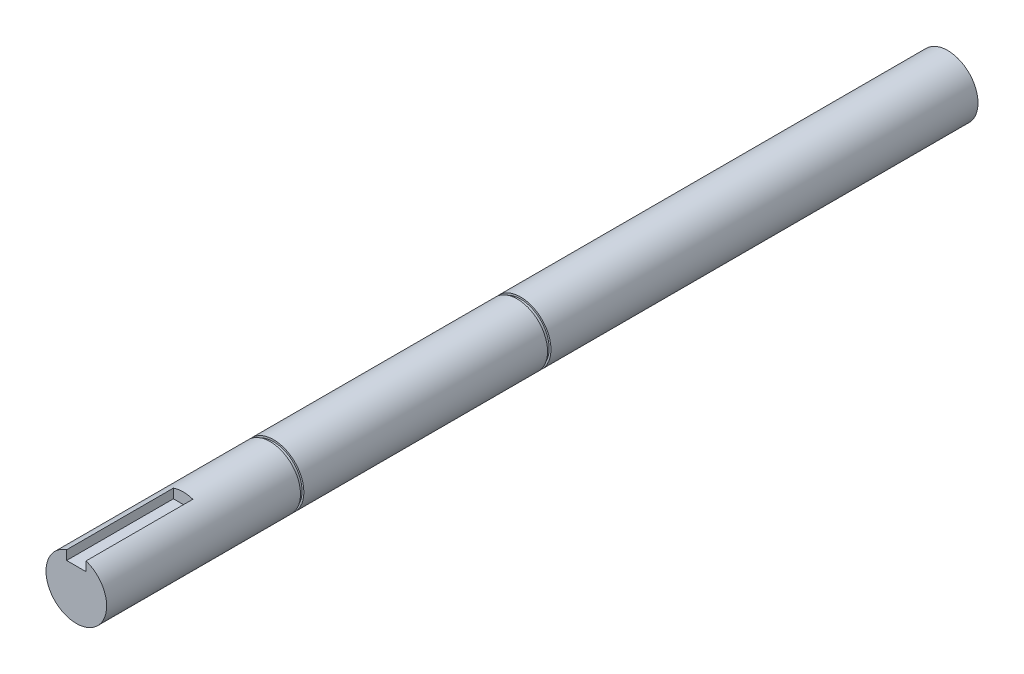
SolidWorks part; units mm, degrees
material "AISI 1020"
ref_plane "Спереди" through (0, 0, 0) normal (0, 0, 1) x (1, 0, 0)
ref_plane "Сверху" through (0, 0, 0) normal (0, 1, 0) x (1, 0, 0)
ref_plane "Справа" through (0, 0, 0) normal (1, 0, 0) x (0, 0, -1)
sketch "Эскиз1" plane through (0, 0, 0) normal (0, 0, 1) x (1, 0, 0)
  circle A0 centre (0, 0) radius 12.5 construction
  circle A1 centre (0, 0) radius 12.5
extrude "Бобышка-Вытянуть1" add sketch "Эскиз1" against normal blind 359 contours A1
sketch "Эскиз2" plane through (0, 0, 0) normal (0, 0, 1) x (1, 0, 0)
  line L0 (-4, 16.5) -> (-4, 8)
  line L1 (-4, 8) -> (4, 8)
  line L2 (4, 8) -> (4, 16.5)
  line L3 (4, 16.5) -> (-4, 16.5)
  line L4 (4, 8.5) -> (4, 16.5) construction
  line L5 (-4, 8.5) -> (4, 8.5) construction
  dimension "D1" = 0.5
extrude "Вырез-Вытянуть1" cut sketch "Эскиз2" against normal up to surface (44 mm away)
sketch "Эскиз3" plane through (0, 0, 0) normal (1, 0, 0) x (0, 0, -1)
  line L0 (-1000, 0) -> (49000, 0) construction
  line L1 (81.25, -11.75) -> (81.25, 11.75) construction
  line L2 (181.65, 14.1459) -> (183.05, 14.1459)
  line L3 (181.65, 14.1459) -> (181.65, 11.75)
  line L4 (181.65, 11.75) -> (183.05, 11.75)
  line L5 (183.05, 14.1459) -> (183.05, 11.75)
  line L6 (81.25, 11.75) -> (80.05, 11.75) construction
  line L12 (182.85, 11.75) -> (181.65, 11.75) construction
  line L19 (181.65, 14.1459) -> (181.65, -13.1541) construction
  line L20 (182.85, 14.1459) -> (181.65, 14.1459) construction
  line L21 (182.85, 16.45) -> (182.85, -16.45) construction
  line L23 (81.25, 14.0128) -> (79.85, 14.0128)
  line L24 (81.25, 14.0128) -> (81.25, 11.75)
  line L25 (81.25, 11.75) -> (79.85, 11.75)
  line L26 (79.85, 14.0128) -> (79.85, 11.75)
  line L27 (80.05, -29.5) -> (80.05, 29.5) construction
  dimension "D1" = 0.2
  dimension "D2" = 0.2
revolve "Вырез-Повернуть1" cut sketch "Эскиз3" angle 360 about L0
sketch "Эскиз4" [suppressed] plane through (0, 0, 0) normal (1, 0, 0) x (0, 0, -1)
  line L0 (-1000, 0) -> (49000, 0) construction
  line L1 (79.55, -14.1298) -> (80.75, -14.1298) construction
  line L2 (80.75, -11.75) -> (80.85, -11.75)
  line L3 (80.75, -11.75) -> (80.75, -14.1298)
  line L4 (80.75, -14.1298) -> (80.85, -14.1298)
  line L5 (80.85, -11.75) -> (80.85, -14.1298)
  line L6 (81.05, -29.5) -> (81.05, 29.5) construction
  line L7 (270.25, 16.45) -> (270.25, -16.45) construction
  line L8 (269.05, -11.75) -> (270.45, -11.75)
  line L9 (269.05, -11.75) -> (269.05, -14.5486)
  line L10 (269.05, -14.5486) -> (270.45, -14.5486)
  line L11 (270.45, -11.75) -> (270.45, -14.5486)
  line L12 (269.05, -14.5486) -> (270.25, -14.5486) construction
  dimension "D1" = 0.2
  dimension "D2" = 0.2
revolve "Вырез-Повернуть2" [suppressed] cut sketch "Эскиз4" angle 360 about L0
equation "\"Длина\"= 359"
